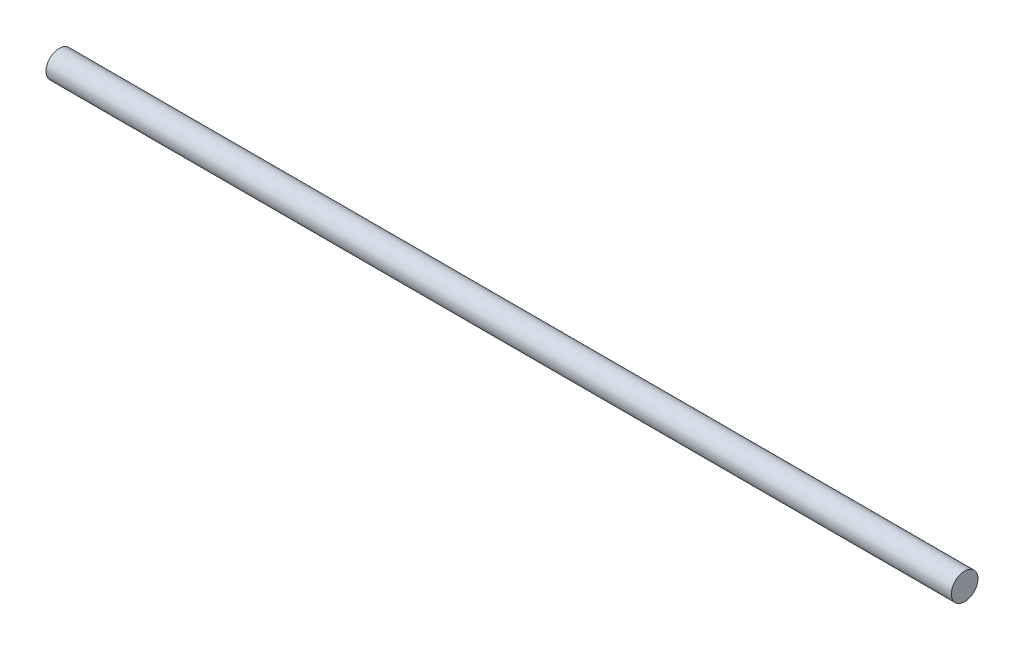
SolidWorks part; units mm, degrees
material "山毛榉"
ref_plane "前视基准面" through (0, 0, 0) normal (0, 0, 1) x (1, 0, 0)
ref_plane "上视基准面" through (0, 0, 0) normal (0, 1, 0) x (1, 0, 0)
ref_plane "右视基准面" through (0, 0, 0) normal (1, 0, 0) x (0, 0, -1)
sketch "草图1" plane through (0, 0, 0) normal (1, 0, 0) x (0, 0, -1)
  circle A0 centre (0, 0) radius 60
  dimension "D1" = 120
extrude "凸台-拉伸1" add sketch "草图1" along normal mid plane 4080
